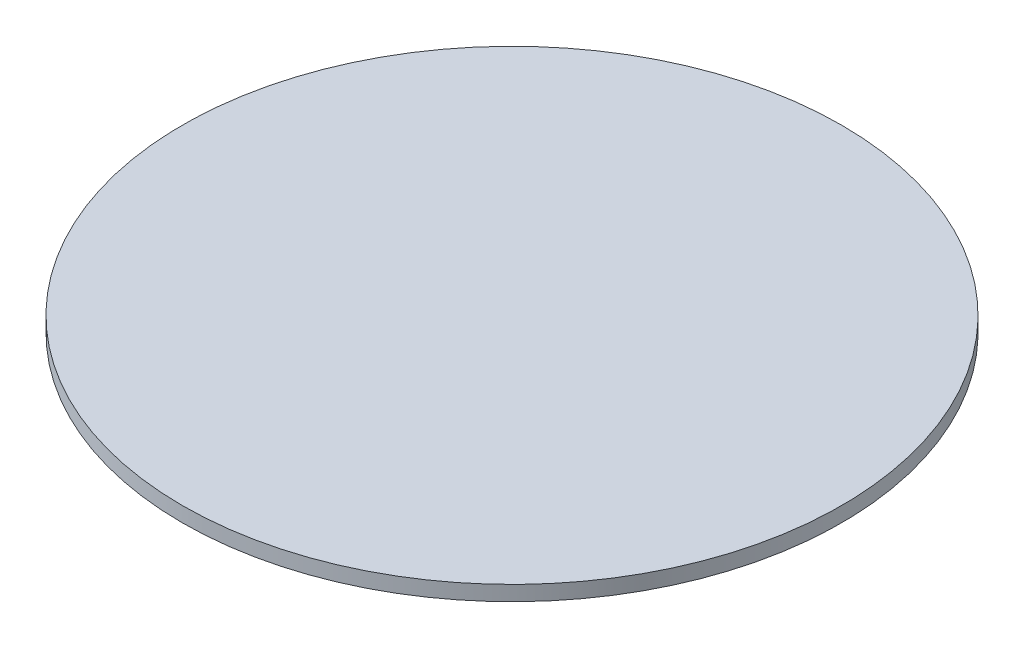
SolidWorks part; units mm, degrees
ref_plane "Front Plane" through (0, 0, 0) normal (0, 0, 1) x (1, 0, 0)
ref_plane "Top Plane" through (0, 0, 0) normal (0, 1, 0) x (1, 0, 0)
ref_plane "Right Plane" through (0, 0, 0) normal (1, 0, 0) x (0, 0, -1)
sketch "Sketch1" plane through (0, 0, 0) normal (0, 1, 0) x (1, 0, 0)
  circle A0 centre (0, 0) radius 69.85
  dimension "D1" = 139.7
extrude "Boss-Extrude1" add sketch "Sketch1" along normal blind 3.175
